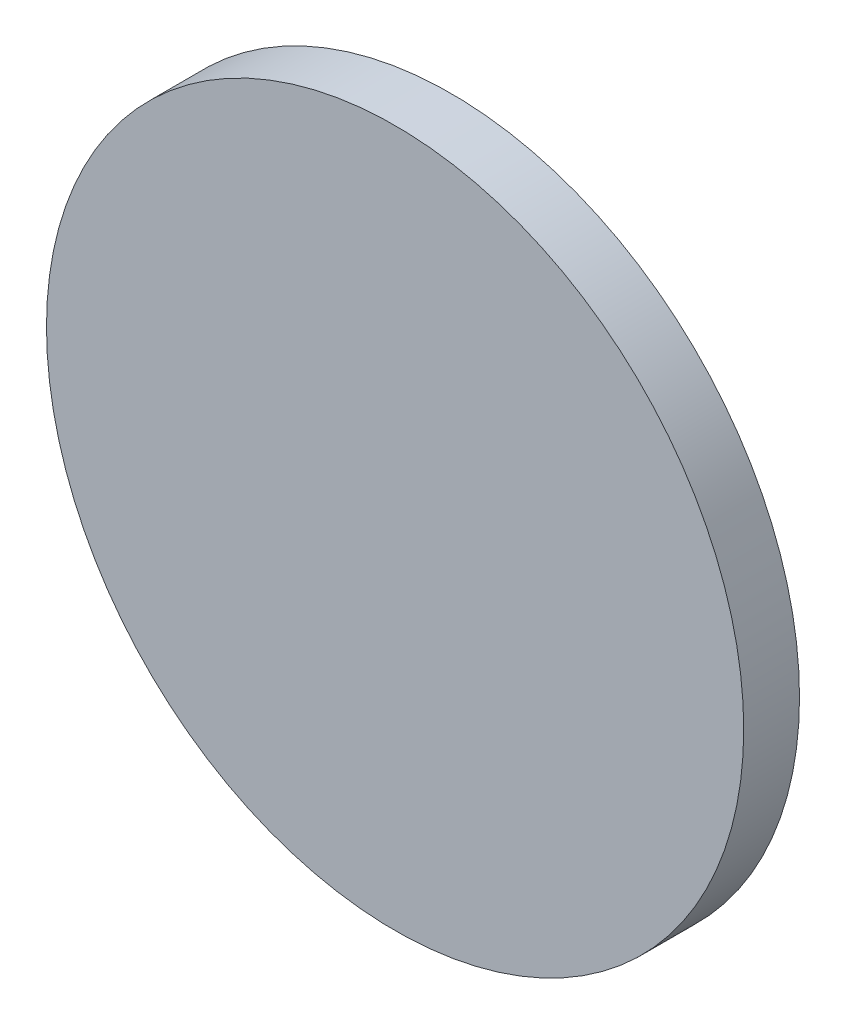
SolidWorks part; units mm, degrees
ref_plane "前视基准面" through (0, 0, 0) normal (0, 0, 1) x (1, 0, 0)
ref_plane "上视基准面" through (0, 0, 0) normal (0, 1, 0) x (1, 0, 0)
ref_plane "右视基准面" through (0, 0, 0) normal (1, 0, 0) x (0, 0, -1)
sketch "草图1" plane through (0, 0, 0) normal (0, 0, 1) x (1, 0, 0)
  circle A0 centre (0, 0) radius 25
  dimension "D1" = 50
extrude "凸台-拉伸1" add sketch "草图1" along normal blind 4 contours A0
